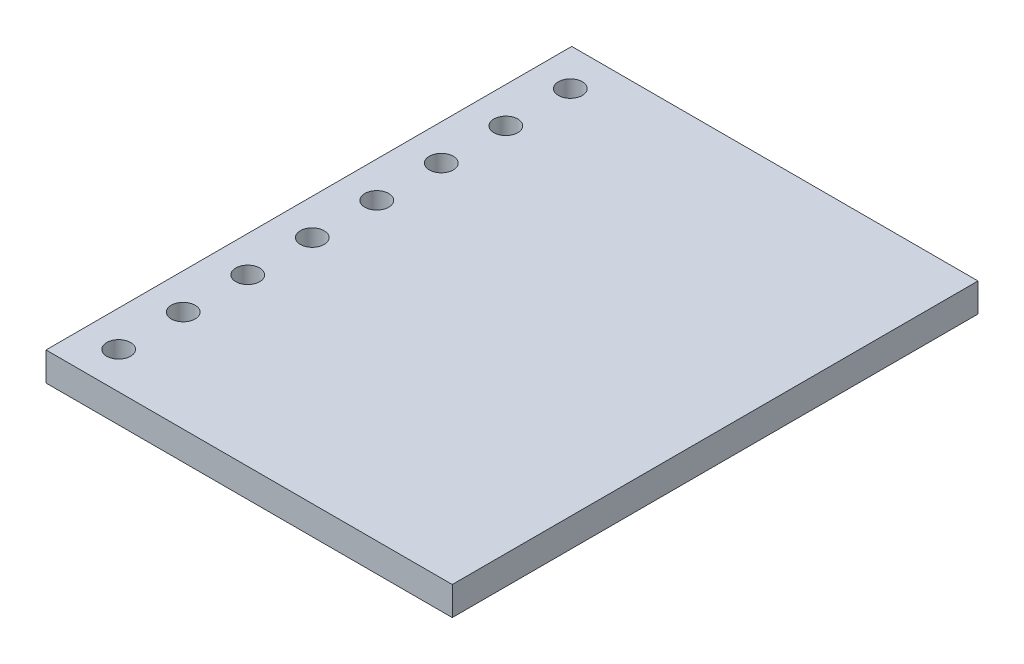
SolidWorks part; units mm, degrees
ref_plane "Front Plane" through (0, 0, 0) normal (0, 0, 1) x (1, 0, 0)
ref_plane "Top Plane" through (0, 0, 0) normal (0, 1, 0) x (1, 0, 0)
ref_plane "Right Plane" through (0, 0, 0) normal (1, 0, 0) x (0, 0, -1)
sketch "Sketch1" plane through (0, 0, 0) normal (0, 1, 0) x (1, 0, 0)
  line L1 (0, 0) -> (17, 0)
  line L2 (0, 0) -> (0, 22)
  line L3 (0, 22) -> (17, 22)
  line L4 (17, 0) -> (17, 22)
  circle A0 centre (1.5, 20.4418) radius 0.5
  circle A1 centre (1.5, 17.7418) radius 0.5
  circle A2 centre (1.5, 15.0418) radius 0.5
  circle A3 centre (1.5, 12.3418) radius 0.5
  circle A4 centre (1.5, 9.6418) radius 0.5
  circle A5 centre (1.5, 6.9418) radius 0.5
  circle A6 centre (1.5, 4.2418) radius 0.5
  circle A7 centre (1.5, 1.5418) radius 0.5
  dimension "D3" = 1
  dimension "D5" = 1.5
  dimension "D1" = 22
  dimension "D2" = 17
  dimension "D4" = 8
extrude "Boss-Extrude1" add sketch "Sketch1" along normal blind 1.2
